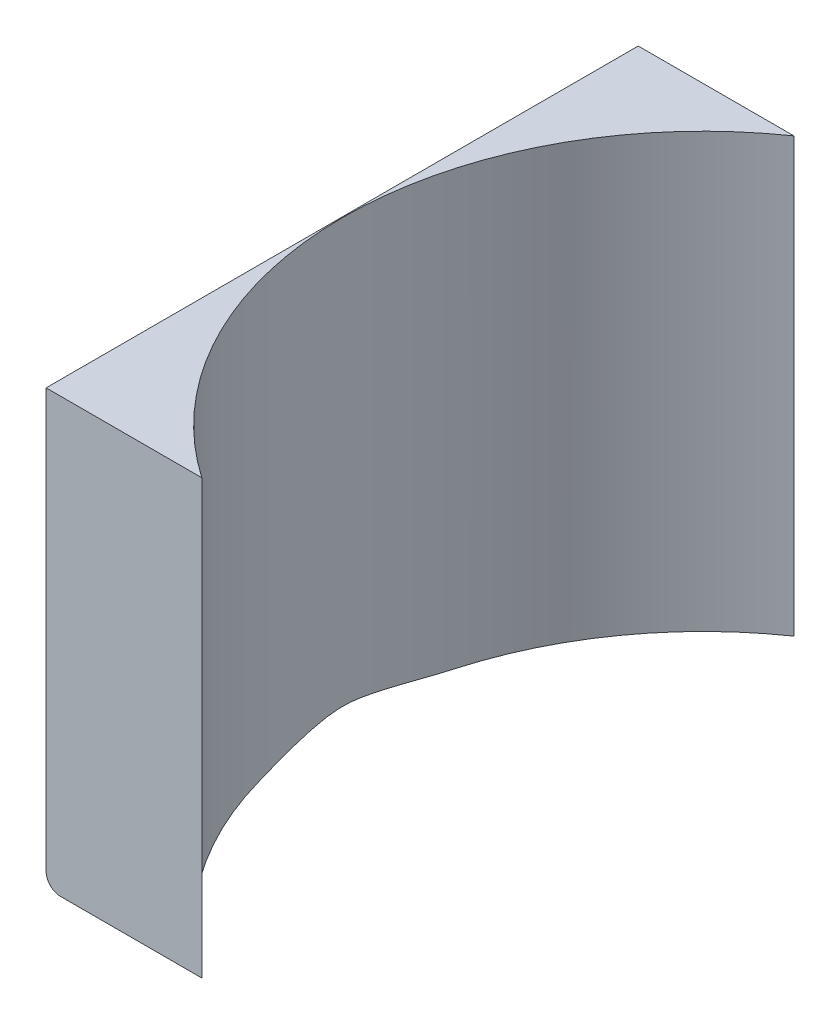
SolidWorks part; units mm, degrees
material "Бутил"
ref_plane "Спереди" through (0, 0, 0) normal (0, 0, 1) x (1, 0, 0)
ref_plane "Сверху" through (0, 0, 0) normal (0, 1, 0) x (1, 0, 0)
ref_plane "Справа" through (0, 0, 0) normal (1, 0, 0) x (0, 0, -1)
other "Configuration Table"
sketch "Эскиз1" plane through (0, 0, 0) normal (0, 1, 0) x (1, 0, 0)
  line L1 (12.5, -20.5) -> (-12.5, -20.5)
  line L2 (12.5, -20.5) -> (12.5, 20.5)
  line L3 (12.5, 20.5) -> (-12.5, 20.5)
  line L4 (-12.5, -20.5) -> (-12.5, 20.5)
  line L5 (12.5, -20.5) -> (-12.5, 20.5) construction
  line L6 (12.5, 20.5) -> (-12.5, -20.5) construction
  point P0 (0, 0)
  dimension "D1" = 25
  dimension "D2" = 41
extrude "Бобышка-Вытянуть1" add sketch "Эскиз1" along normal blind 30
fillet "Скругление1" radius 1 1 edges at (-12.5, 0, 0)
sketch "Эскиз2" plane through (0, 30, 0) normal (0, 1, 0) x (1, 0, 0)
  line L0 (12.5, -20.5) -> (12.5, 20.5) construction
  circle A0 centre (12.5, 0) radius 24.95
  dimension "D1" = 49.9
extrude "Вырез-Вытянуть1" cut sketch "Эскиз2" against normal blind 30
